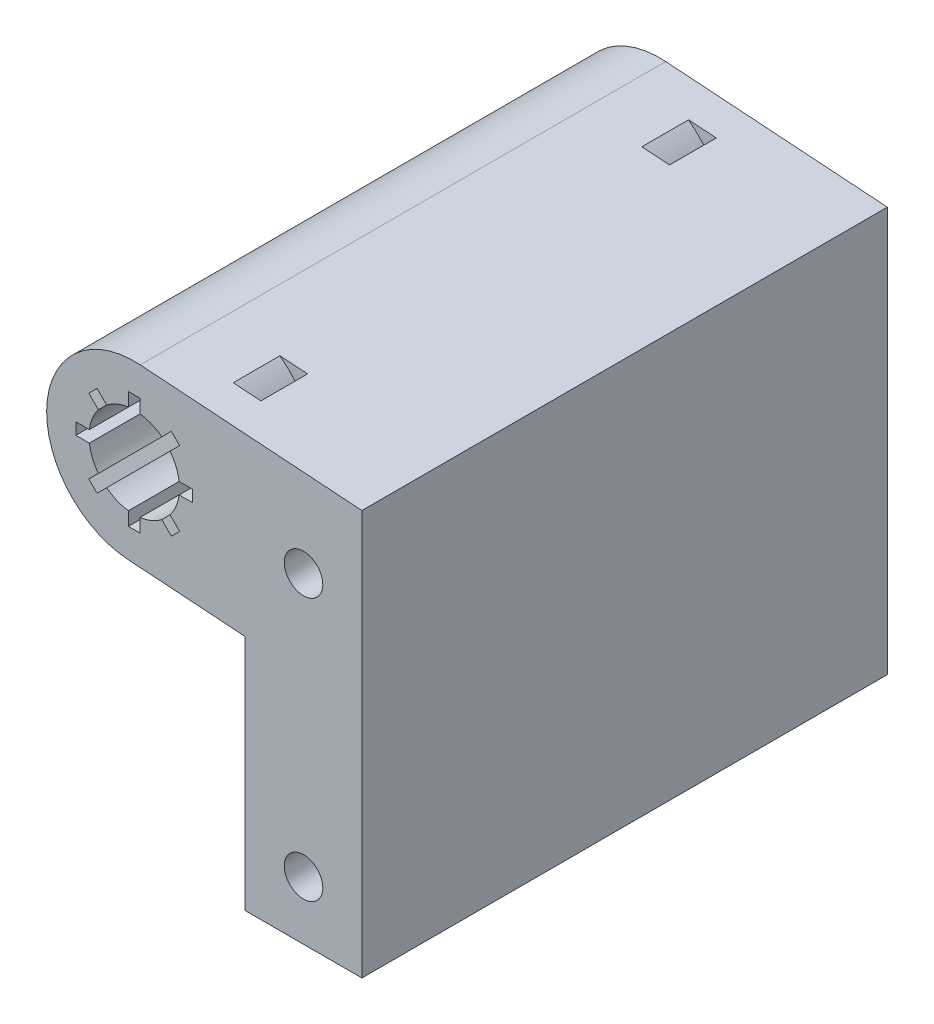
SolidWorks part; units mm, degrees
ref_plane "Front Plane" through (0, 0, 0) normal (0, 0, 1) x (1, 0, 0)
ref_plane "Top Plane" through (0, 0, 0) normal (0, 1, 0) x (1, 0, 0)
ref_plane "Right Plane" through (0, 0, 0) normal (1, 0, 0) x (0, 0, -1)
sketch "Sketch1" plane through (0, 0, 0) normal (0, 0, 1) x (1, 0, 0)
  line L0 (-182, 170) -> (-167.5, 169) construction
  line L1 (-167.5, 169) -> (-167.5, 146.5) construction
  line L2 (-182.516, 162.5178) -> (-172.5, 161.827)
  line L3 (-172.5, 161.827) -> (-172.5, 141.5)
  line L4 (-181.484, 177.4822) -> (-162.5, 176.173)
  line L5 (-162.5, 176.173) -> (-162.5, 141.5)
  line L6 (-172.5, 141.5) -> (-162.5, 141.5)
  line L7 (-167.5, 146.5) -> (-167.5, 141.5) construction
  circle A0 centre (-167.5, 146.5) radius 2.4 construction
  circle A3 centre (-167.5, 146.5) radius 2.4 construction
  circle A4 centre (-167.5, 169) radius 2.4 construction
  arc A5 (-182.516, 162.5178) -> (-181.484, 177.4822) centre (-182, 170) ccw
  dimension "D1" = 7.5
  dimension "D6" = 4.8
  dimension "D3" = 5
  dimension "D4" = 14.5
  dimension "D5" = 23.5
  dimension "D2" = 22.5
  dimension "D7" = 5
  dimension "D8" = 7.5
  dimension "D9" = 5
extrude "Boss-Extrude1" add sketch "Sketch1" along normal blind 45 contours L5 L6 L3 L2 A5 L4
sketch "Sketch2" plane through (0, 0, 0) normal (0, 0, -1) x (-1, 0, 0)
  line L0 (162.5, 176.173) -> (181.484, 177.4822) construction
  line L2 (182.516, 162.5178) -> (172.5, 161.827) construction
  arc A0 (176.5208, 177.1399) -> (177.5529, 162.1755) centre (182, 170) ccw
  arc A1 (181.484, 177.4822) -> (182.516, 162.5178) centre (182, 170) ccw construction
  arc A3 (175.6076, 178.3299) -> (176.8117, 160.8714) centre (182, 170) ccw
  arc A4 (176.5208, 177.1399) -> (175.6076, 178.3299) centre (176.0642, 177.7349) ccw
  arc A5 (177.5529, 162.1755) -> (176.8117, 160.8714) centre (177.1823, 161.5234) cw
  point P8 (177.508, 162.1724)
  point P9 (0, 0)
  point P10 (0, 0)
  point P11 (182.1468, 160.2513)
  point P17 (0, 0)
  dimension "D1" = 9
  dimension "D2" = 1.5
extrude "Cut-Extrude1" cut sketch "Sketch2" against normal mid plane 4 from offset 5 offset against normal yes
ref_plane "Plane1" through (0, 0, 22.5) normal (0, 0, -1) x (-1, 0, 0)
mirror "Mirror1" about plane through (0, 0, 22.5) normal (0, 0, -1) of "Cut-Extrude1"
hole_wizard "M4x0.7 Tapped Hole1" positions "Sketch3" profile "Sketch4" tap size "M4x0.7" standard "ANSI Metric" end condition through all
sketch "Sketch3" plane through (0, 0, 45) normal (0, 0, 1) x (1, 0, 0)
  point P0 (-167.5, 169)
  point P3 (-167.5, 146.5)
sketch "Sketch4" plane through (-167.5, 169, 45) normal (1, 0, 0) x (0, -1, 0)
  line L0 (0, 0) -> (0, 45)
  line L1 (0, 45) -> (1.65, 45)
  line L2 (1.65, 45) -> (1.65, 0)
  line L5 (1.65, 0) -> (0, 0)
  line L11 (0, -6.35) -> (0, 107.95) construction
  dimension "Thru Tap Drill Dia." = 3.3
  dimension "Thru Tap Drill Depth" = 45
cosmetic thread "Hole Thread1" parameters "D2"=4
cosmetic thread "Hole Thread2" parameters "D2"=4
sketch "Sketch5" plane through (0, 0, 45) normal (0, 0, 1) x (1, 0, 0)
  circle A0 centre (-182, 170) radius 7.5
extrude "Boss-Extrude2" add sketch "Sketch5" against normal through all
sketch "Sketch6" plane through (0, 0, 45) normal (0, 0, 1) x (1, 0, 0)
  circle A0 centre (-182, 170) radius 3.875
  dimension "D1" = 7.75
extrude "Cut-Extrude2" cut sketch "Sketch6" against normal through all
sketch "Sketch7" plane through (0, 0, 0) normal (0, 0, -1) x (-1, 0, 0)
  line L0 (181.4341, 177.4788) -> (182.4661, 162.5143)
  line L1 (181.4341, 177.4788) -> (181.5339, 177.4857)
  line L2 (182.4661, 162.5143) -> (182.5659, 162.5212)
  line L3 (181.5339, 177.4857) -> (182.5659, 162.5212)
  line L4 (162.5, 176.173) -> (181.484, 177.4822) construction
  line L5 (182.516, 162.5178) -> (172.5, 161.827) construction
  line L6 (182.516, 162.5178) -> (181.484, 177.4822) construction
  point P10 (181.484, 177.4822)
  dimension "D1" = 0.1
extrude "Cut-Extrude3" [suppressed] cut sketch "Sketch7" against normal through all
sketch "Sketch8" plane through (0, 0, 45) normal (0, 0, 1) x (1, 0, 0)
  line L0 (-182.5, 165) -> (-182.5, 175)
  line L1 (-182.5, 165) -> (-181.5, 165)
  line L2 (-182.5, 175) -> (-181.5, 175)
  line L3 (-181.5, 165) -> (-181.5, 175)
  line L4 (-182, 175) -> (-182, 165) construction
  line L5 (-182.5, 170) -> (-181.5, 170) construction
  line L6 (-185.8891, 166.818) -> (-178.818, 173.8891)
  line L7 (-185.8891, 166.818) -> (-185.182, 166.1109)
  line L8 (-178.818, 173.8891) -> (-178.1109, 173.182)
  line L9 (-185.182, 166.1109) -> (-178.1109, 173.182)
  line L10 (-178.4645, 173.5355) -> (-185.5355, 166.4645) construction
  line L11 (-182.3536, 170.3536) -> (-181.6464, 169.6464) construction
  line L12 (-187, 170.5) -> (-177, 170.5)
  line L13 (-187, 170.5) -> (-187, 169.5)
  line L14 (-177, 170.5) -> (-177, 169.5)
  line L15 (-187, 169.5) -> (-177, 169.5)
  line L16 (-177, 170) -> (-187, 170) construction
  line L17 (-182, 170.5) -> (-182, 169.5) construction
  line L18 (-185.182, 173.8891) -> (-178.1109, 166.818)
  line L19 (-185.182, 173.8891) -> (-185.8891, 173.182)
  line L20 (-178.1109, 166.818) -> (-178.818, 166.1109)
  line L21 (-185.8891, 173.182) -> (-178.818, 166.1109)
  line L22 (-178.4645, 166.4645) -> (-185.5355, 173.5355) construction
  line L23 (-181.6464, 170.3536) -> (-182.3536, 169.6464) construction
  circle A0 centre (-182, 170) radius 3.875 construction
  point P0 (-186.6989, 170)
  point P1 (-182, 170)
  point P3 (-182, 170)
  point P4 (-182, 170)
  point P7 (-182, 170)
  circle M21 centre (-182, 170) radius 3.875
  dimension "D1" = 45
  dimension "D2" = 1
  dimension "D3" = 10
extrude "Cut-Extrude4" cut sketch "Sketch8" against normal through all contours L21 L20 L18 M21 | L1 L3 L0 M21 | L7 L9 L6 M21 | L13 L15 L12 M21 | L19 L21 L18 M21 | L3 L2 L0 M21 | L9 L8 L6 M21 | L15 L14 L12 M21
